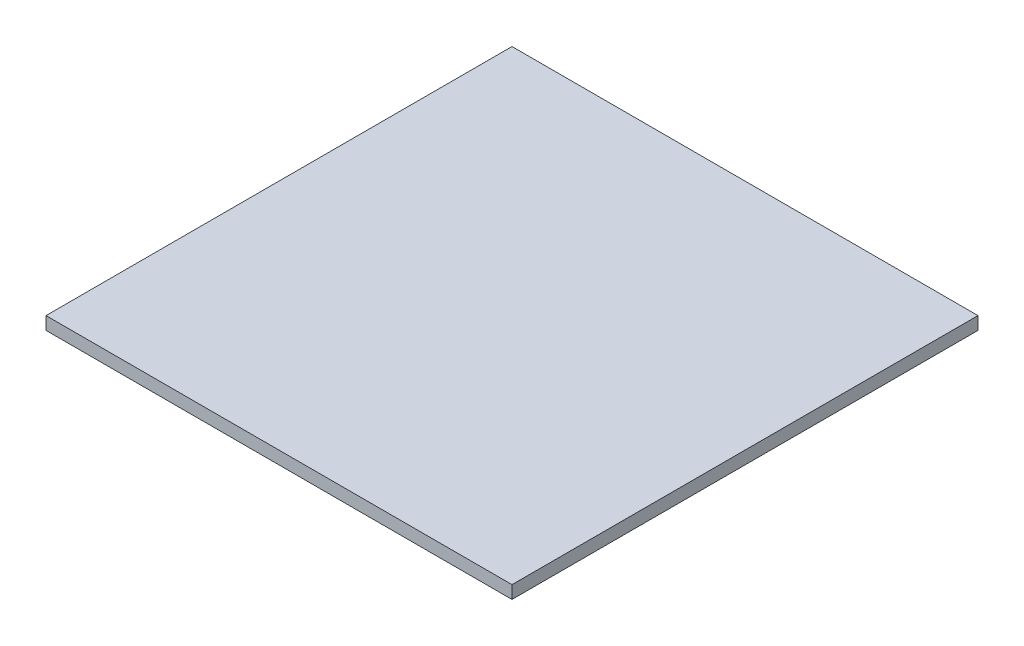
SolidWorks part; units mm, degrees
material "Pine"
ref_plane "Front Plane" through (0, 0, 0) normal (0, 0, 1) x (1, 0, 0)
ref_plane "Top Plane" through (0, 0, 0) normal (0, 1, 0) x (1, 0, 0)
ref_plane "Right Plane" through (0, 0, 0) normal (1, 0, 0) x (0, 0, -1)
sketch "Sketch1" plane through (0, 0, 0) normal (0, 1, 0) x (1, 0, 0)
  line L1 (-215.9, -215.9) -> (215.9, -215.9)
  line L2 (-215.9, -215.9) -> (-215.9, 215.9)
  line L3 (-215.9, 215.9) -> (215.9, 215.9)
  line L4 (215.9, -215.9) -> (215.9, 215.9)
  line L5 (-215.9, -215.9) -> (215.9, 215.9) construction
  line L6 (-215.9, 215.9) -> (215.9, -215.9) construction
  point P0 (0, 0)
  dimension "D1" = 431.8
  dimension "D2" = 431.8
extrude "Boss-Extrude1" add sketch "Sketch1" along normal blind 11.9062
